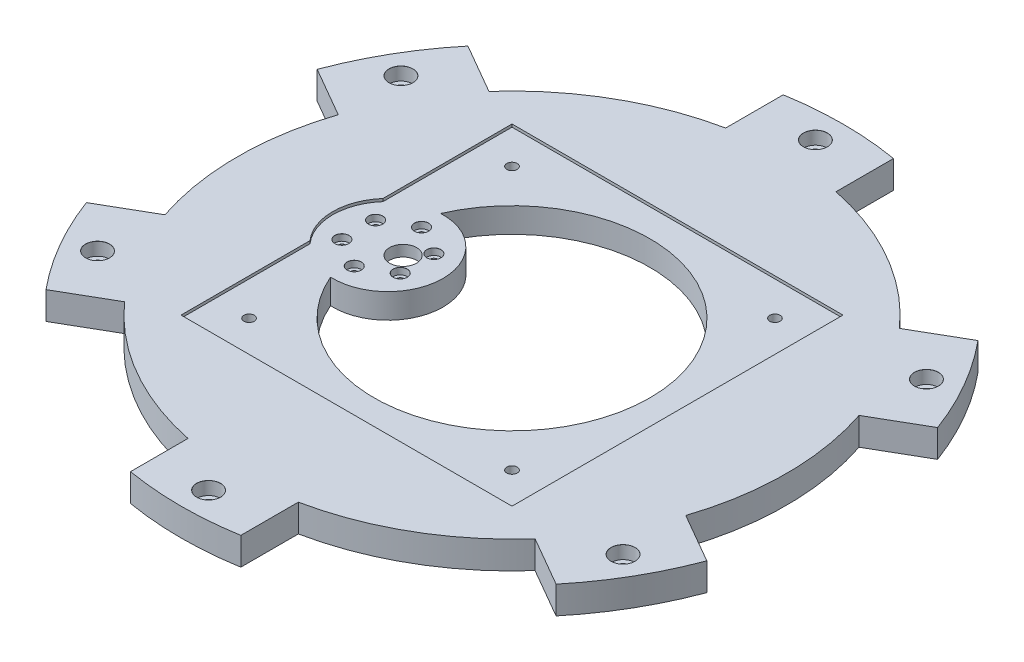
SolidWorks part; units mm, degrees
ref_plane "Front Plane" through (0, 0, 0) normal (0, 0, 1) x (1, 0, 0)
ref_plane "Top Plane" through (0, 0, 0) normal (0, 1, 0) x (1, 0, 0)
ref_plane "Right Plane" through (0, 0, 0) normal (1, 0, 0) x (0, 0, -1)
sketch "Sketch1" plane through (0, 0, 0) normal (0, 1, 0) x (1, 0, 0)
  line L0 (0, 0) -> (0, 149.8525) construction
  line L1 (-25.4, 123.7859) -> (-25.4, 150.2684)
  line L2 (25.4, 123.7859) -> (25.4, 150.2684)
  line L3 (94.5017, 83.89) -> (117.4363, 97.1313)
  line L4 (119.9017, 39.8959) -> (142.8363, 53.1372)
  line L5 (119.9017, -39.8959) -> (142.8363, -53.1372)
  line L6 (94.5017, -83.89) -> (117.4363, -97.1313)
  line L7 (25.4, -123.7859) -> (25.4, -150.2684)
  line L8 (-25.4, -123.7859) -> (-25.4, -150.2684)
  line L9 (-94.5017, -83.89) -> (-117.4363, -97.1313)
  line L10 (-119.9017, -39.8959) -> (-142.8363, -53.1372)
  line L11 (-119.9017, 39.8959) -> (-142.8363, 53.1372)
  line L12 (-94.5017, 83.89) -> (-117.4363, 97.1313)
  arc A0 (-25.4, 123.7859) -> (-94.5017, 83.89) centre (0, 0) ccw
  arc A1 (25.4, 150.2684) -> (-25.4, 150.2684) centre (0, 0) ccw
  arc A2 (142.8363, 53.1372) -> (117.4363, 97.1313) centre (0, 0) ccw
  arc A3 (117.4363, -97.1313) -> (142.8363, -53.1372) centre (0, 0) ccw
  arc A4 (-25.4, -150.2684) -> (25.4, -150.2684) centre (0, 0) ccw
  arc A5 (-142.8363, -53.1372) -> (-117.4363, -97.1313) centre (0, 0) ccw
  arc A6 (-117.4363, 97.1313) -> (-142.8363, 53.1372) centre (0, 0) ccw
  arc A7 (-119.9017, 39.8959) -> (-119.9017, -39.8959) centre (0, 0) ccw
  arc A8 (94.5017, 83.89) -> (25.4, 123.7859) centre (0, 0) ccw
  arc A9 (119.9017, -39.8959) -> (119.9017, 39.8959) centre (0, 0) ccw
  arc A10 (25.4, -123.7859) -> (94.5017, -83.89) centre (0, 0) ccw
  arc A11 (-94.5017, -83.89) -> (-25.4, -123.7859) centre (0, 0) ccw
  point P32 (0, 0)
  dimension "D1" = 252.73
  dimension "D2" = 304.8
  dimension "D3" = 50.8
  dimension "D4" = 6
extrude "Boss-Extrude1" add sketch "Sketch1" along normal blind 12.7 contours A0 L12 A6 L11 A7 L10 A5 L9 A11 L8 A4 L7 A10 L6 A3 L5 A9 L4 A2 L3 A8 L2 A1 L1
sketch "Sketch2" plane through (0, 0, 0) normal (0, 1, 0) x (1, 0, 0)
  circle A0 centre (0, 0) radius 63.5
  dimension "D1" = 127
extrude "Cut-Extrude2" cut sketch "Sketch2" along normal up to surface (12.7 mm away) up to face at (0, 12.7, 0)
sketch "Sketch3" plane through (0, 12.7, 0) normal (0, 1, 0) x (1, 0, 0)
  line L0 (-76.2, 16.8005) -> (-76.2, 76.2)
  line L1 (-76.2, -76.2) -> (76.2, -76.2)
  line L2 (-76.2, -76.2) -> (-76.2, -16.8005)
  line L3 (-76.2, 76.2) -> (76.2, 76.2)
  line L4 (76.2, -76.2) -> (76.2, 76.2)
  line L5 (-76.2, -76.2) -> (76.2, 76.2) construction
  line L6 (-76.2, 76.2) -> (76.2, -76.2) construction
  arc A0 (-76.2, 16.8005) -> (-76.2, -16.8005) centre (-57.15, 0) ccw
  point P0 (0, 0)
  dimension "D3" = 57.15
  dimension "D2" = 50.8
  dimension "D1" = 152.4
extrude "Cut-Extrude3" cut sketch "Sketch3" against normal blind 1.27
sketch "Sketch4" plane through (0, 11.43, 0) normal (0, 1, 0) x (1, 0, 0)
  line L0 (-60.5282, -60.5282) -> (60.5282, 60.5282) construction
  line L1 (-60.5282, 60.5282) -> (60.5282, -60.5282) construction
  circle A4 centre (-60.5282, 60.5282) radius 2.4003
  circle A5 centre (-60.5282, -60.5282) radius 2.4003
  circle A6 centre (60.5282, -60.5282) radius 2.4003
  circle A7 centre (60.5282, 60.5282) radius 2.4003
  point P0 (0, 0)
  point P1 (0, 0)
  dimension "D3" = 4.8006
  dimension "D4" = 4.8006
  dimension "D5" = 4.8006
  dimension "D6" = 4.8006
  dimension "D1" = 121.0564
  dimension "D2" = 121.0564
extrude "Cut-Extrude4" cut sketch "Sketch4" against normal through all both and the other way through all
sketch "Sketch5" plane through (0, 12.7, 0) normal (0, 1, 0) x (1, 0, 0)
  circle A0 centre (0, 0) radius 139.7 construction
  point P3 (0, 139.7)
  point P7 (120.9837, 69.85)
  point P8 (120.9837, -69.85)
  point P9 (0, -139.7)
  point P10 (-120.9837, -69.85)
  point P11 (-120.9837, 69.85)
  point P12 (0, 0)
  dimension "D1" = 279.4
  dimension "D2" = 6
hole_wizard "CBORE for M6 SHCS2" positions "Sketch5" profile "Sketch6" counterbore size "M6" standard "ANSI Metric" end condition through all
sketch "Sketch6" plane through (0, 12.7, 0) normal (1, 0, 0) x (0, 0, 1)
  line L0 (0, 0) -> (0, 12.7)
  line L1 (0, 12.7) -> (3.3, 12.7)
  line L3 (3.3, 12.7) -> (3.3, 6)
  line L4 (5.5, 6) -> (3.3, 6)
  line L5 (5.5, 6) -> (5.5, 0.025)
  line L6 (5.5, 0.025) -> (5.525, 0)
  line L7 (5.525, 0) -> (0, 0)
  line L8 (-5.5, 0.025) -> (-5.525, 0) construction
  line L11 (0, -6.35) -> (0, 107.95) construction
  dimension "Thru Hole Dia." = 6.6
  dimension "Thru Hole Depth" = 12.7
  dimension "C'Bore Dia." = 11
  dimension "C'Bore Depth" = 6
  dimension "Near C'Sink Dia." = 11.05
  dimension "Near C'Sink Angle" = 90
sketch "Sketch7" plane through (0, 0, 0) normal (0, -1, 0) x (1, 0, 0)
  line L0 (0, 0) -> (-78.137, 0) construction
  circle A0 centre (-57.15, 0) radius 25.4
  circle A2 centre (0, 0) radius 63.5 construction
  dimension "D1" = 50.8
  dimension "D2" = 57.15
extrude "Boss-Extrude2" add sketch "Sketch7" against normal up to surface (11.43 mm away) contours A0 up to face at (60.5282, 11.43, -58.1279)
sketch "Sketch8" plane through (0, 0, 0) normal (0, -1, 0) x (-1, 0, 0)
  line L0 (0, 0) -> (85.9005, 0) construction
  circle A0 centre (57.15, 0) radius 18.542
  dimension "D2" = 57.15
  dimension "D1" = 37.084
extrude "Cut-Extrude5" cut sketch "Sketch8" against normal blind 6.35
sketch "Sketch9" plane through (0, 11.43, 0) normal (0, -1, 0) x (1, 0, 0)
  line L0 (0, 0) -> (-70.0247, 0) construction
  circle A0 centre (-57.15, 0) radius 15.5 construction
  point P8 (-57.15, 15.5)
  point P10 (-43.7266, 7.75)
  point P11 (-43.7266, -7.75)
  point P12 (-57.15, -15.5)
  point P13 (-70.5734, -7.75)
  point P14 (-70.5734, 7.75)
  point P15 (-57.15, 0)
  dimension "D1" = 30.9999
  dimension "D3" = 57.15
  dimension "D2" = 6
hole_wizard "CBORE for M3 SHCS1" positions "Sketch9" profile "Sketch10" counterbore size "M3" standard "ANSI Metric"
sketch "Sketch10" plane through (-70.5734, 11.43, 7.75) normal (1, 0, 0) x (0, 0, 1)
  line L0 (0, 0) -> (0, 6.1015)
  line L1 (0, 6.1015) -> (1.7, 5.08)
  line L2 (1.7, 5.08) -> (1.7, 3)
  line L3 (1.7, 3) -> (3.25, 3)
  line L5 (3.25, 3) -> (3.25, 0.025)
  line L6 (3.25, 0.025) -> (3.275, 0)
  line L7 (3.275, 0) -> (0, 0)
  line L8 (-3.25, 0.025) -> (-3.275, 0) construction
  line L10 (0, 6.1015) -> (-1.7, 5.08) construction
  line L11 (0, -6.35) -> (0, 107.95) construction
  dimension "Hole Dia." = 3.4
  dimension "Hole Depth" = 5.08
  dimension "C'Bore Dia." = 6.5
  dimension "C'Bore Depth" = 3
  dimension "Near C'Sink Dia." = 6.55
  dimension "Near C'Sink Angle" = 90
  dimension "Drill Angle" = 118
sketch "Sketch11" plane through (0, 0, 0) normal (0, -1, 0) x (1, 0, 0)
  line L0 (0, 0) -> (-72.3792, 0) construction
  circle A0 centre (-57.15, 0) radius 7 construction
  circle A3 centre (-50.15, 0) radius 6.223
  dimension "D3" = 57.15
  dimension "D1" = 14
  dimension "D2" = 12.446
extrude "Cut-Extrude6" cut sketch "Sketch11" against normal up to surface (11.43 mm away)
equation "\"lazy_susan_bottom_hole\"=0.189"
equation "\"D5@Sketch4\"=\"lazy_susan_bottom_hole\""
equation "\"D6@Sketch4\"=\"lazy_susan_bottom_hole\""
equation "\"D3@Sketch4\"=\"lazy_susan_bottom_hole\""
equation "\"D4@Sketch4\"=\"lazy_susan_bottom_hole\""
equation "\"motor mount offset\"=2.25"
equation "\"D2@Sketch7\"=\"motor mount offset\""
equation "\"D2@Sketch8\"=\"motor mount offset\""
equation "\"D3@Sketch9\"=\"motor mount offset\""
equation "\"D3@Sketch11\"=\"motor mount offset\""
equation "\"D3@Sketch3\"=\"motor mount offset\""
